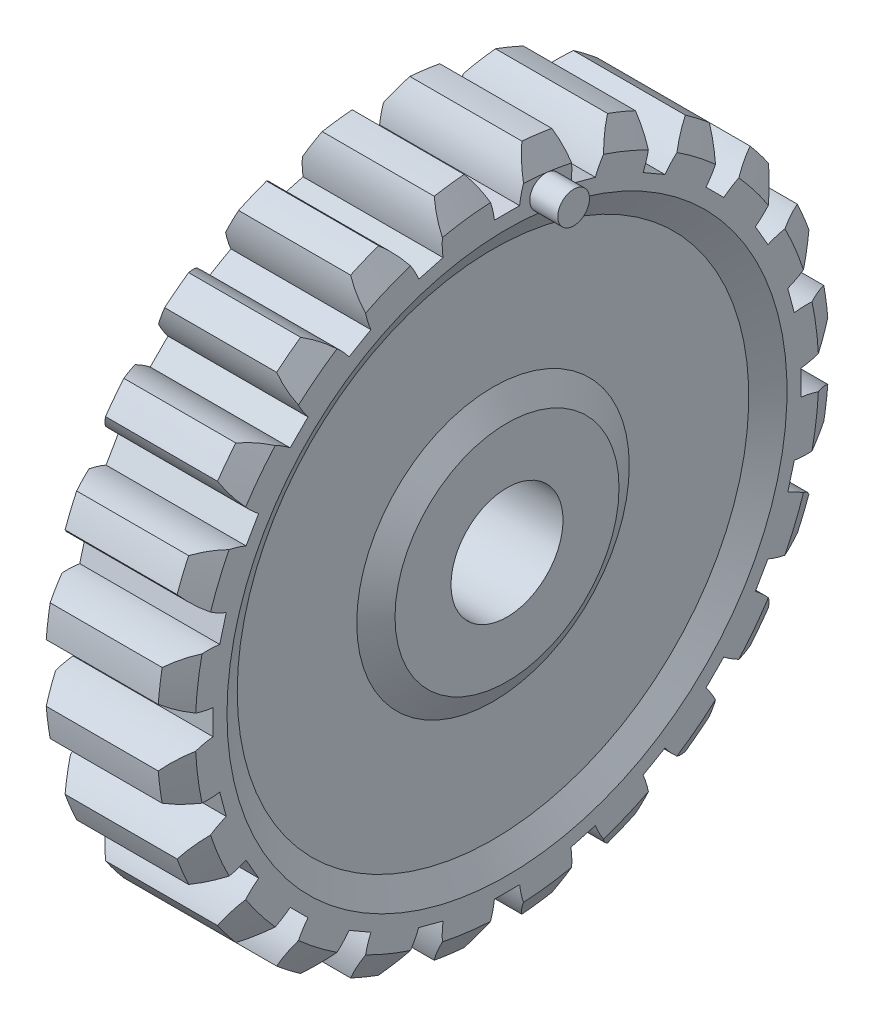
SolidWorks part; units mm, degrees
ref_plane "Front Plane" through (0, 0, 0) normal (0, 0, 1) x (1, 0, 0)
ref_plane "Top Plane" through (0, 0, 0) normal (0, 1, 0) x (1, 0, 0)
ref_plane "Right Plane" through (0, 0, 0) normal (1, 0, 0) x (0, 0, -1)
sketch "Sketch1" plane through (0, 0, 0) normal (0, 0, 1) x (1, 0, 0)
  line L0 (0, 0) -> (0, 80.811) construction
  line L1 (0, 0) -> (64.8204, 0) construction
  line L2 (15.875, 12.7) -> (-15.875, 12.7)
  line L3 (-15.875, 12.7) -> (-15.875, 25.4)
  line L4 (-15.875, 25.4) -> (-12.7, 30.8993)
  line L5 (-12.7, 30.8993) -> (-12.7, 58.0007)
  line L6 (-12.7, 58.0007) -> (-15.875, 63.5)
  line L7 (-15.875, 63.5) -> (-15.875, 70.7007)
  line L8 (-15.875, 70.7007) -> (-12.7, 76.2)
  line L9 (-12.7, 76.2) -> (12.7, 76.2)
  line L10 (15.875, 70.7007) -> (12.7, 76.2)
  line L11 (15.875, 63.5) -> (15.875, 70.7007)
  line L12 (12.7, 58.0007) -> (15.875, 63.5)
  line L13 (12.7, 30.8993) -> (12.7, 58.0007)
  line L14 (15.875, 25.4) -> (12.7, 30.8993)
  line L15 (15.875, 12.7) -> (15.875, 25.4)
  point P6 (0, 0)
  point P14 (-15.548, 63.5)
  point P15 (0, 0)
  point P17 (0, 76.2)
  point P23 (0, 12.7)
  dimension "D1" = 30
  dimension "D2" = 12.7
  dimension "D3" = 25.4
  dimension "D4" = 63.5
  dimension "D5" = 76.2
  dimension "D6" = 15.875
  dimension "D7" = 12.7
revolve "Revolve1" add sketch "Sketch1" angle 360 about L1
sketch "Sketch3" plane through (15.875, 0, 0) normal (1, 0, 0) x (0, 0, -1)
  line L0 (0, 0) -> (0, 76.2) construction
  line L1 (-2.8575, 66.675) -> (2.8575, 66.675)
  circle A0 centre (0, 0) radius 76.2 construction
  arc A1 (-6.5405, 75.9188) -> (-2.8575, 66.675) centre (-21.7818, 64.4906) cw
  arc A2 (2.8575, 66.675) -> (6.5405, 75.9188) centre (21.7818, 64.4906) cw
  arc A3 (6.5405, 75.9188) -> (-6.5405, 75.9188) centre (0, 0) ccw
  dimension "D2" = 19.05
  dimension "D1" = 13.081
  dimension "D3" = 5.715
  dimension "D4" = 66.675
extrude "Cut-Extrude1" cut sketch "Sketch3" against normal through all
pattern_circular "CirPattern1" count 24 over 360 about axis through (0, 0, 0) along (1, 0, 0) of "Cut-Extrude1"
sketch "Sketch4" plane through (15.875, 0, 0) normal (1, 0, 0) x (0, 0, -1)
  line L0 (0, 0) -> (9.2283, 70.0959) construction
  circle A0 centre (0, 0) radius 63.5 construction
  arc A1 (14.6618, 69.1638) -> (3.7387, 70.6018) centre (0, 0) ccw construction
  circle A2 centre (0, 0) radius 63.5
  arc A3 (14.6618, 69.1638) -> (3.7387, 70.6018) centre (0, 0) ccw
  circle A4 centre (8.7584, 66.5263) radius 3.6004
extrude "Boss-Extrude2" add sketch "Sketch4" along normal blind 6.35 contours A4 L0 | L0 A4
